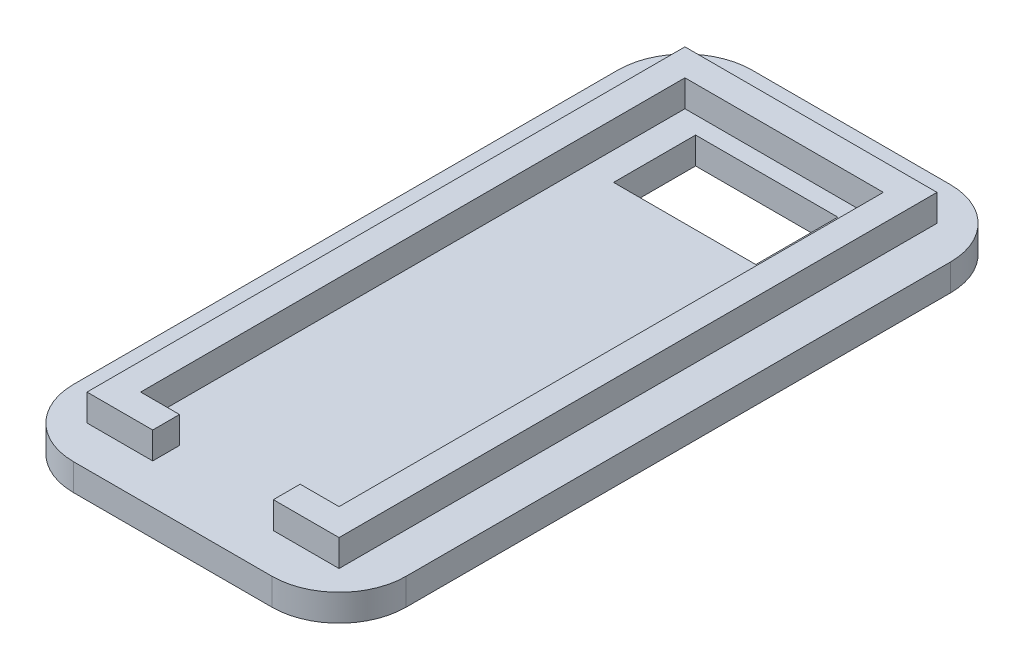
SolidWorks part; units mm, degrees
ref_plane "Front Plane" through (0, 0, 0) normal (0, 0, 1) x (1, 0, 0)
ref_plane "Top Plane" through (0, 0, 0) normal (0, 1, 0) x (1, 0, 0)
ref_plane "Right Plane" through (0, 0, 0) normal (1, 0, 0) x (0, 0, -1)
sketch "Sketch1" plane through (0, 0, 0) normal (0, 1, 0) x (1, 0, 0)
  line L0 (-12.4, 25.3) -> (-12.4, -25.3)
  line L1 (-9.4, 22.3) -> (9.4, 22.3) construction
  line L2 (-9.4, 22.3) -> (-9.4, -22.3) construction
  line L3 (-9.4, -22.3) -> (9.4, -22.3) construction
  line L4 (9.4, 22.3) -> (9.4, -22.3) construction
  line L5 (-9.4, 22.3) -> (9.4, -22.3) construction
  line L6 (-9.4, -22.3) -> (9.4, 22.3) construction
  line L7 (-12.4, -25.3) -> (12.4, -25.3)
  line L8 (12.4, 25.3) -> (12.4, -25.3)
  line L9 (-12.4, 25.3) -> (12.4, 25.3)
  point P0 (0, 0)
  dimension "D2" = 18.8
  dimension "D3" = 44.6
  dimension "D1" = 3
extrude "Boss-Extrude1" add sketch "Sketch1" along normal blind 2
sketch "Sketch2" plane through (0, 2, 0) normal (0, 1, 0) x (1, 0, 0)
  line L4 (7.4, 20.3) -> (-7.4, 20.3)
  line L5 (-7.4, 20.3) -> (-7.4, -20.3)
  line L6 (-7.4, -20.3) -> (7.4, -20.3)
  line L7 (7.4, -20.3) -> (7.4, 20.3)
  line L8 (9.4, 22.3) -> (-9.4, 22.3)
  line L9 (-9.4, 22.3) -> (-9.4, -22.3)
  line L10 (-9.4, -22.3) -> (9.4, -22.3)
  line L11 (9.4, -22.3) -> (9.4, 22.3)
  line L12 (9.4, 22.3) -> (-9.4, 22.3)
  line L13 (-9.4, 22.3) -> (-9.4, -22.3)
  line L14 (-9.4, -22.3) -> (9.4, -22.3)
  line L15 (9.4, -22.3) -> (9.4, 22.3)
  line L16 (0, -25.3) -> (0, -22.3) construction
  line L17 (-4.5, -20.3) -> (4.5, -20.3)
  line L18 (-4.5, -20.3) -> (-4.5, -22.3)
  line L19 (-4.5, -22.3) -> (4.5, -22.3)
  line L20 (4.5, -20.3) -> (4.5, -22.3)
  line L21 (-12.4, -25.3) -> (12.4, -25.3) construction
  dimension "D3" = 9
  dimension "D1" = 3
  dimension "D2" = 2
extrude "Boss-Extrude2" add sketch "Sketch2" along normal blind 2 contours L6 L20 L14 L15 L12 L13 L18 L5 L4 L7
sketch "Sketch3" plane through (0, 2, 0) normal (0, 1, 0) x (1, 0, 0)
  line L16 (0, 20) -> (0, -25.3) construction
  line L17 (-12.4, -25.3) -> (12.4, -25.3) construction
  line L18 (-5.305, 19) -> (-5.305, 12.88)
  line L19 (-5.005, 18.7) -> (5.005, 18.7) construction
  line L20 (-5.005, 18.7) -> (-5.005, 13.18) construction
  line L21 (4.5, -20) -> (7.1, -20)
  line L22 (-7.1, -20) -> (-4.5, -20)
  line L23 (7.1, -20) -> (7.1, 20)
  line L24 (7.1, 20) -> (-7.1, 20)
  line L25 (-7.1, 20) -> (-7.1, -20)
  line L26 (4.5, -20) -> (7.1, -20)
  line L27 (-7.1, -20) -> (-4.5, -20)
  line L28 (7.1, -20) -> (7.1, 20)
  line L29 (7.1, 20) -> (-7.1, 20)
  line L30 (-7.1, 20) -> (-7.1, -20)
  line L31 (-5.005, 13.18) -> (5.005, 13.18) construction
  line L32 (5.005, 18.7) -> (5.005, 13.18) construction
  line L33 (-5.005, 18.7) -> (5.005, 13.18) construction
  line L34 (-5.005, 13.18) -> (5.005, 18.7) construction
  line L35 (-5.305, 12.88) -> (5.305, 12.88)
  line L36 (5.305, 19) -> (5.305, 12.88)
  line L37 (-5.305, 19) -> (5.305, 19)
  point P4 (0, 15.94)
  dimension "D3" = 5.52
  dimension "D4" = 10.01
  dimension "D5" = 1
  dimension "D1" = 0.3
  dimension "D2" = 0.3
extrude "Cut-Extrude1" cut sketch "Sketch3" against normal through all contours L18 L35 L36 L37
fillet "Fillet1" radius 5 4 edges at (-12.4, 1, 25.3) (12.4, 1, 25.3) (12.4, 1, -25.3) (-12.4, 1, -25.3)
